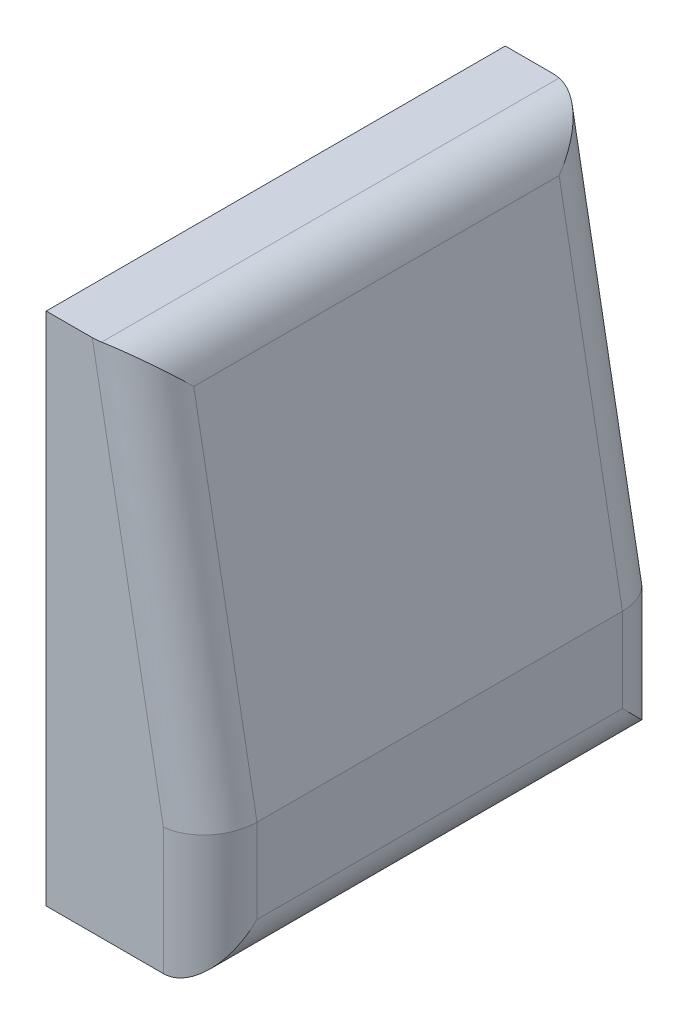
SolidWorks part; units mm, degrees
ref_plane "Front Plane" through (0, 0, 0) normal (0, 0, 1) x (1, 0, 0)
ref_plane "Top Plane" through (0, 0, 0) normal (0, 1, 0) x (1, 0, 0)
ref_plane "Right Plane" through (0, 0, 0) normal (1, 0, 0) x (0, 0, -1)
sketch "Sketch1" plane through (0, 0, 0) normal (0, 0, 1) x (1, 0, 0)
  line L0 (0, 1100) -> (0, 0)
  line L1 (0, 0) -> (350, 0)
  line L2 (350, 0) -> (350, 280)
  line L3 (350, 280) -> (200, 1100)
  line L4 (200, 1100) -> (0, 1100)
  dimension "D1" = 1100
  dimension "D2" = 200
  dimension "D3" = 350
  dimension "D4" = 280
extrude "Boss-Extrude1" add sketch "Sketch1" along normal mid plane 980
fillet "Fillet1" radius 100 6 edges at (350, 140, -490) (275, 690, -490) (350, 0, 0) (350, 140, 490) (275, 690, 490) (200, 1100, 0)
